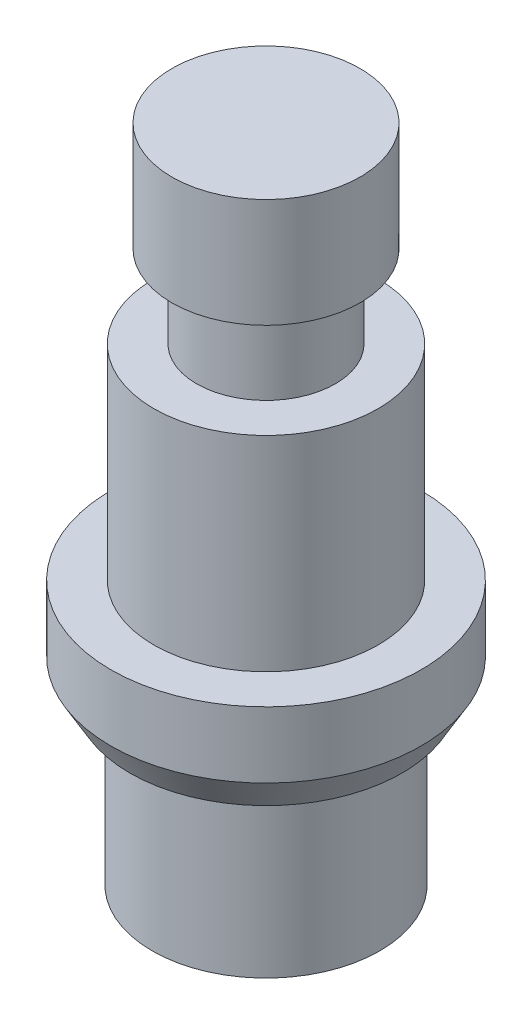
SolidWorks part; units mm, degrees
ref_plane "Спереди" through (0, 0, 0) normal (0, 0, 1) x (1, 0, 0)
ref_plane "Сверху" through (0, 0, 0) normal (0, 1, 0) x (1, 0, 0)
ref_plane "Справа" through (0, 0, 0) normal (1, 0, 0) x (0, 0, -1)
sketch "Sketch1" plane through (0, 0, 0) normal (0, 1, 0) x (1, 0, 0)
  circle A0 centre (0, 0) radius 4.7
  dimension "D1" = 9.4
extrude "Boss-Extrude1" add sketch "Sketch1" along normal blind 20
sketch "Sketch2" plane through (0, 0, 0) normal (0, -1, 0) x (1, 0, 0)
  circle A0 centre (0, 0) radius 3.45
  dimension "D1" = 6.9
extrude "Cut-Extrude1" cut sketch "Sketch2" against normal blind 5 flip side to cut
sketch "Sketch3" plane through (0, 5, 0) normal (0, -1, 0) x (1, 0, 0)
  circle A0 centre (0, 0) radius 4.7
sketch "Sketch4" plane through (0, 20, 0) normal (0, 1, 0) x (1, 0, 0)
  circle A0 centre (0, 0) radius 3.4
  dimension "D1" = 6.8
extrude "Cut-Extrude2" cut sketch "Sketch4" against normal blind 12 flip side to cut
sketch "Sketch5" plane through (0, 20, 0) normal (0, 1, 0) x (1, 0, 0)
  circle A0 centre (0, 0) radius 2.85
  dimension "D1" = 5.7
extrude "Cut-Extrude3" cut sketch "Sketch5" against normal blind 3.3 flip side to cut
sketch "Sketch7" plane through (0, 16.7, 0) normal (0, 1, 0) x (1, 0, 0)
  circle A0 centre (0, 0) radius 2.1
  dimension "D1" = 4.2
extrude "Cut-Extrude4" cut sketch "Sketch7" against normal blind 2.5 flip side to cut
chamfer "Chamfer1" distance 1 angle 30 1 edges at (0, 5, -4.7)
